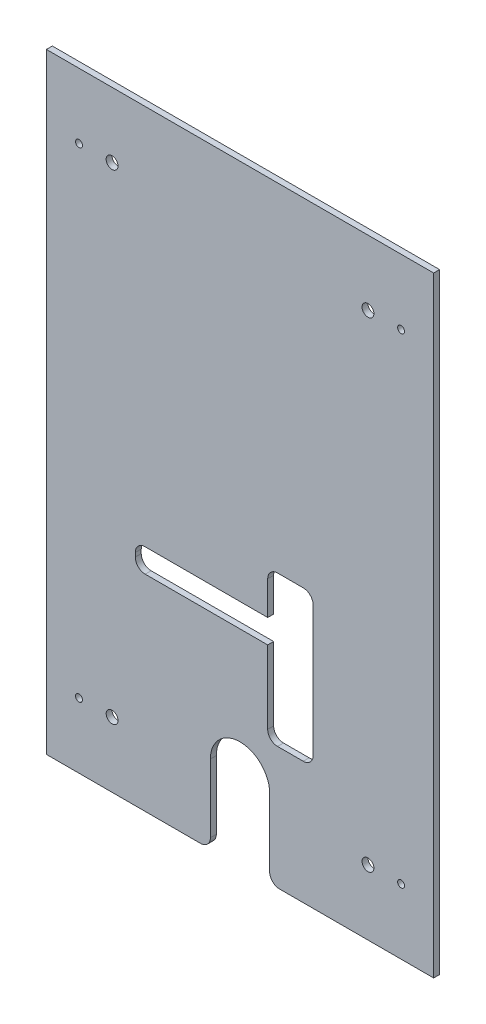
SolidWorks part; units mm, degrees
ref_plane "Plan de face" through (0, 0, 0) normal (0, 0, 1) x (1, 0, 0)
ref_plane "Plan de dessus" through (0, 0, 0) normal (0, 1, 0) x (1, 0, 0)
ref_plane "Plan de droite" through (0, 0, 0) normal (1, 0, 0) x (0, 0, -1)
sketch "Esquisse1" plane through (0, 0, 0) normal (0, 0, 1) x (1, 0, 0)
  line L0 (0, 154.5) -> (0, -154.5) construction
  line L1 (98, 154.5) -> (-98, 154.5)
  line L2 (98, 154.5) -> (98, -154.5)
  line L3 (98, -154.5) -> (-98, -154.5)
  line L4 (-98, 154.5) -> (-98, -154.5)
  line L5 (98, 154.5) -> (-98, -154.5) construction
  line L6 (98, -154.5) -> (-98, 154.5) construction
  line L7 (-98, 0) -> (98, 0) construction
  line L8 (81.5, 121.5) -> (64.75, 121.5) construction
  circle A0 centre (-81.5, 121.5) radius 1.75
  circle A1 centre (81.5, 121.5) radius 1.75
  circle A2 centre (81.5, -121.5) radius 1.75
  circle A3 centre (-81.5, -121.5) radius 1.75
  circle A4 centre (64.75, 121.5) radius 3
  circle A6 centre (-64.75, 121.5) radius 3
  circle A7 centre (-64.75, -121.5) radius 3
  circle A8 centre (64.75, -121.5) radius 3
  point P0 (0, 0)
  dimension "D2" = 3.5
  dimension "D7" = 6
  dimension "D1" = 163
  dimension "D3" = 309
  dimension "D4" = 196
  dimension "D5" = 33
  dimension "D6" = 16.75
extrude "Boss.-Extru.1" add sketch "Esquisse1" along normal blind 3
sketch "Esquisse2" plane through (0, 0, 3) normal (0, 0, 1) x (1, 0, 0)
  line L0 (0, -154.5) -> (0, -115) construction
  line L1 (-98, -154.5) -> (98, -154.5) construction
  line L2 (-15, -154.5) -> (-15, -115)
  line L3 (15, -154.5) -> (15, -115)
  arc A0 (-15, -154.5) -> (15, -154.5) centre (0, -154.5) ccw
  arc A1 (15, -115) -> (-15, -115) centre (0, -115) ccw
  point P5 (0, -134.75)
  dimension "D2" = 15
  dimension "D1" = 39.5
extrude "Enlèv. mat.-Extru.1" cut sketch "Esquisse2" against normal up to next
fillet "Congé1" radius 5 2 edges at (15, -154.5, 1.5) (-15, -154.5, 1.5)
sketch "Esquisse3" plane through (0, 0, 3) normal (0, 0, 1) x (1, 0, 0)
  line L0 (-98, -154.5) -> (-20, -154.5) construction
  line L1 (-53, -38.5) -> (14, -38.5)
  line L2 (-53, -38.5) -> (-53, -50.5)
  line L3 (-53, -50.5) -> (14, -50.5)
  line L4 (14, -38.5) -> (14, -50.5) construction
  line L6 (-98, 154.5) -> (-98, -154.5) construction
  line L7 (14, -16.5) -> (14, -38.5)
  line L8 (37, -16.5) -> (14, -16.5)
  line L9 (37, -16.5) -> (37, -92.5)
  line L10 (37, -92.5) -> (14, -92.5)
  line L11 (14, -16.5) -> (14, -92.5) construction
  line L12 (14, -50.5) -> (14, -92.5)
  dimension "D1" = 12
  dimension "D2" = 116
  dimension "D3" = 67
  dimension "D4" = 45
  dimension "D5" = 23
  dimension "D6" = 22
  dimension "D7" = 42
extrude "Enlèv. mat.-Extru.2" cut sketch "Esquisse3" against normal through all
fillet "Congé2" radius 5 6 edges at (-53, -50.5, 1.5) (-53, -38.5, 1.5) (14, -92.5, 1.5) (37, -92.5, 1.5) (37, -16.5, 1.5) (14, -16.5, 1.5)
